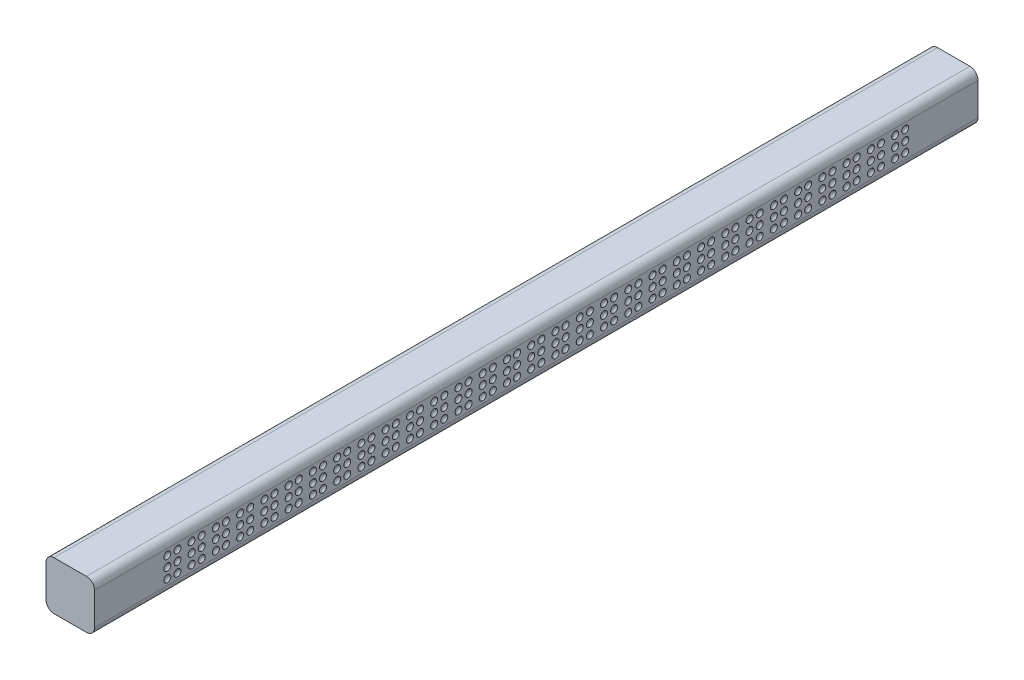
SolidWorks part; units mm, degrees
ref_plane "Front plane" through (0, 0, 0) normal (0, 0, 1) x (1, 0, 0)
ref_plane "Top plane" through (0, 0, 0) normal (0, 1, 0) x (1, 0, 0)
ref_plane "Right Plane" through (0, 0, 0) normal (1, 0, 0) x (0, 0, -1)
sketch "Sketch2" plane through (0, 0, 0) normal (0, 0, 1) x (1, 0, 0)
  line L1 (-4, 6) -> (4, 6)
  line L2 (-6, 4) -> (-6, -4)
  line L3 (-4, -6) -> (4, -6)
  line L4 (6, 4) -> (6, -4)
  arc A0 (-4, 6) -> (-6, 4) centre (-4, 4) ccw
  arc A1 (4, 6) -> (6, 4) centre (4, 4) cw
  arc A2 (4, -6) -> (6, -4) centre (4, -4) ccw
  arc A3 (-6, -4) -> (-4, -6) centre (-4, -4) ccw
  point P8 (6, 0)
  point P16 (0, 6)
  dimension "D3" = 2
  dimension "D1" = 12
extrude "Boss-Extrude1" add sketch "Sketch2" along normal blind 218.5
ref_plane "Plane1" through (0, 0, 18) normal (0, 0, -1) x (-1, 0, 0)
sketch "Sketch5" [suppressed] plane through (0, 0, 18) normal (0, 0, -1) x (-1, 0, 0)
  line L0 (-6, -2.5) -> (-6, -3.4)
  line L1 (-6, -3.4) -> (-5.7696, -3.4)
  line L2 (-5.7696, -3.4) -> (-5.3, -2.5866)
  line L5 (-5.3, -2.5) -> (-6, -2.5)
  line L6 (-6, -2.5) -> (-5.25, -2.5) construction
  line L7 (-5.3, -2.5866) -> (-5.3, -2.5)
  line L8 (-6, -4) -> (-6, 4) construction
  dimension "D1" = 60
  dimension "D2" = 0.9
  dimension "D3" = 0.75
  dimension "D4" = 0.05
  dimension "D5" = 2.5
revolve "Cut-Revolve2" [suppressed] cut sketch "Sketch5" angle 360 about L6
sketch "Sketch4" plane through (0, 0, 18) normal (0, 0, -1) x (-1, 0, 0)
  line L0 (-6, -3.366) -> (-6, -1.634)
  line L1 (-6.5, -2.5) -> (-6.5, -1.634) construction
  line L2 (-6, -4) -> (-6, 4) construction
  arc A0 (-6, -1.634) -> (-6, -3.366) centre (-6.5, -2.5) cw
  point P3 (-5.5, -2.5)
  dimension "D2" = 1
  dimension "D1" = 0.5
  dimension "D3" = 2.5
revolve "Cut-Revolve1" cut sketch "Sketch4" angle 360 about L1
pattern_linear "LPattern5" [suppressed] count 3 spacing 2.5 count 2 spacing 2.5
pattern_linear "LPattern3" count 3 spacing 2.5 along (0, 1, 0) count 2 spacing 2.5 along (0, 0, 1) of "Cut-Revolve1"
pattern_linear "LPattern7" [suppressed] count 31 spacing 6
pattern_linear "LPattern4" count 31 spacing 6 along (0, 0, 1) of "Cut-Revolve1", "LPattern3"
